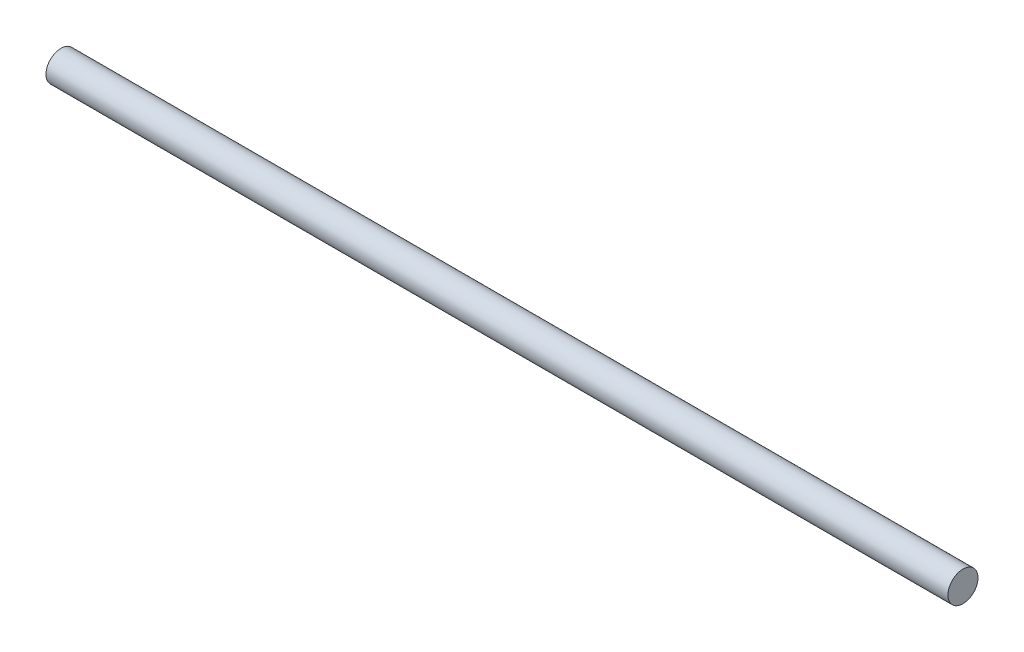
SolidWorks part; units mm, degrees
material "6061-T6 (SS)"
ref_plane "Front Plane" through (0, 0, 0) normal (0, 0, 1) x (1, 0, 0)
ref_plane "Top Plane" through (0, 0, 0) normal (0, 1, 0) x (1, 0, 0)
ref_plane "Right Plane" through (0, 0, 0) normal (1, 0, 0) x (0, 0, -1)
sketch "Sketch1" plane through (0, 0, 0) normal (1, 0, 0) x (0, 0, -1)
  circle A0 centre (0, 0) radius 9.525
  dimension "D1" = 19.05
extrude "Boss-Extrude1" add sketch "Sketch1" along normal blind 571.5
